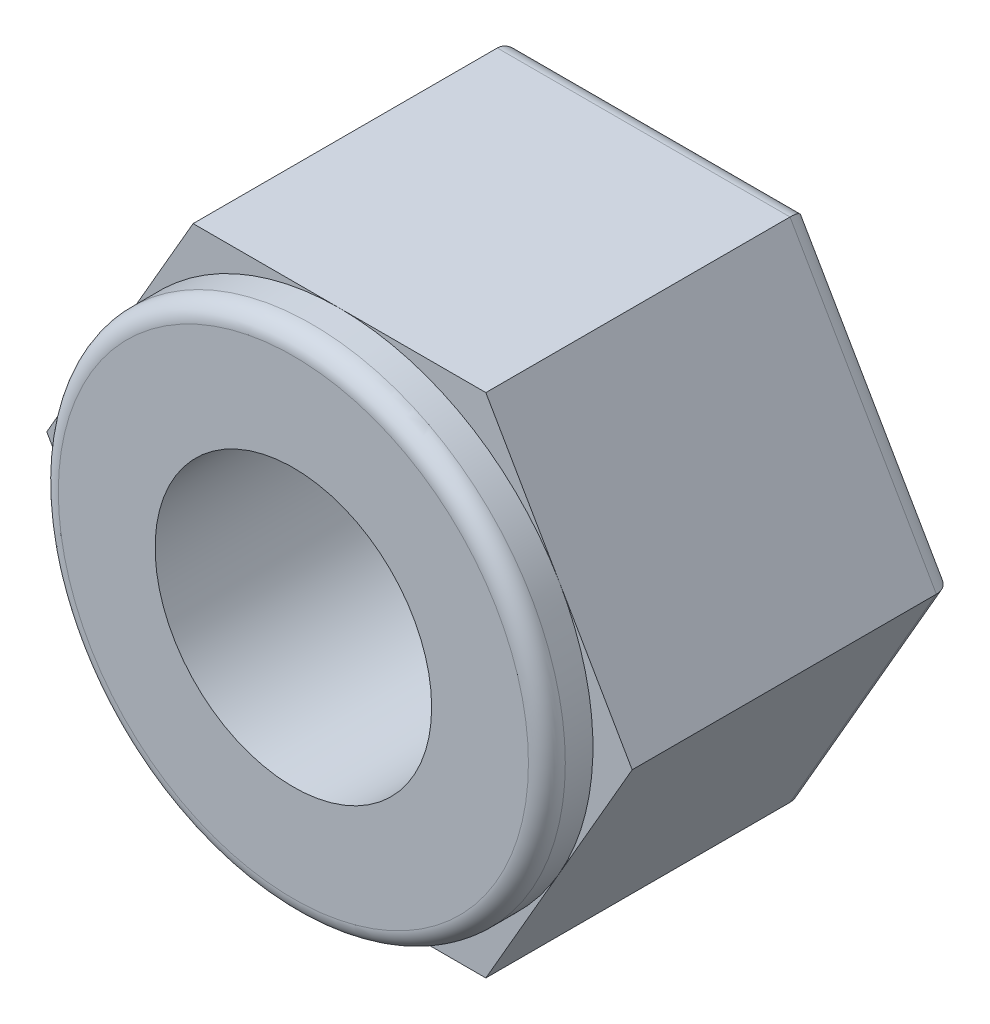
SolidWorks part; units mm, degrees
ref_plane "前视基准面" through (0, 0, 0) normal (0, 0, 1) x (1, 0, 0)
ref_plane "上视基准面" through (0, 0, 0) normal (0, 1, 0) x (1, 0, 0)
ref_plane "右视基准面" through (0, 0, 0) normal (1, 0, 0) x (0, 0, -1)
sketch "草图1" plane through (0, 0, 0) normal (0, 0, 1) x (1, 0, 0)
  line L1 (3.1754, 0) -> (1.5877, 2.75)
  line L2 (1.5877, 2.75) -> (-1.5877, 2.75)
  line L3 (-1.5877, 2.75) -> (-3.1754, 0)
  line L4 (-3.1754, 0) -> (-1.5877, -2.75)
  line L5 (-1.5877, -2.75) -> (1.5877, -2.75)
  line L6 (1.5877, -2.75) -> (3.1754, 0)
  circle A0 centre (0, 0) radius 2.75 construction
  circle A1 centre (0, 0) radius 1.5
  dimension "D2" = 3
  dimension "D1" = 5.5
extrude "凸台-拉伸1" add sketch "草图1" along normal blind 3.5
sketch "草图2" plane through (0, 0, 3.5) normal (0, 0, 1) x (1, 0, 0)
  circle A0 centre (0, 0) radius 2.75
  circle A1 centre (0, 0) radius 1.5
extrude "凸台-拉伸2" add sketch "草图2" along normal blind 0.5
fillet "圆角4" radius 0.2 1 edges at (2.75, 0, 4)
fillet "圆角5" radius 0.2 6 edges at (-2.3816, -1.375, 0) (-2.3816, 1.375, 0) (0, 2.75, 0) (2.3816, 1.375, 0) (2.3816, -1.375, 0) (0, -2.75, 0)
